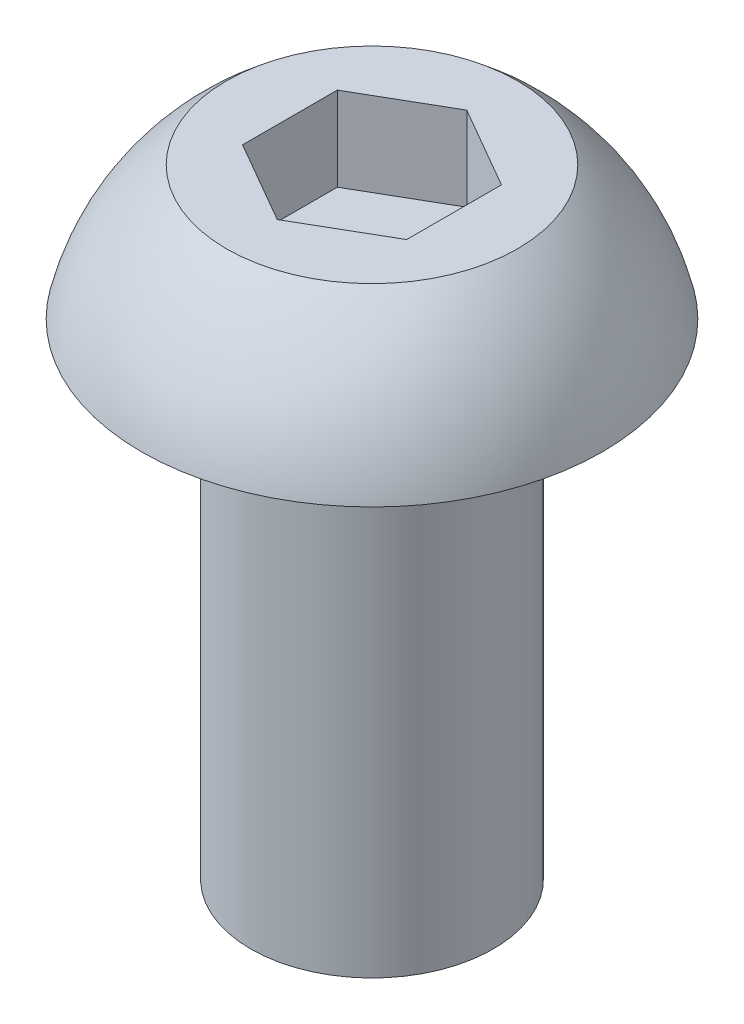
SolidWorks part; units mm, degrees
material "普通碳钢"
ref_plane "前视基准面" through (0, 0, 0) normal (0, 0, 1) x (1, 0, 0)
ref_plane "上视基准面" through (0, 0, 0) normal (0, 1, 0) x (1, 0, 0)
ref_plane "右视基准面" through (0, 0, 0) normal (1, 0, 0) x (0, 0, -1)
sketch "草图1" plane through (0, 0, 0) normal (0, 0, 1) x (1, 0, 0)
  line L0 (0, 2.3045) -> (-1.8, 2.3045)
  line L1 (0, 2.3045) -> (0, -5.3455)
  line L2 (-2.85, 0.6545) -> (-1.5, 0.6545)
  line L3 (0, -5.3455) -> (-1.5, -5.3455)
  line L4 (-1.5, -5.3455) -> (-1.5, 0.6545)
  line L5 (0, 0) -> (0, 50000) construction
  arc A0 (-1.8, 2.3045) -> (-2.85, 0.6545) centre (0, 0) ccw
  dimension "da" = 3.6
  dimension "dk" = 5.7
  dimension "d" = 3
  dimension "k" = 1.65
  dimension "L" = 6
revolve "旋转1" add sketch "草图1" angle 360 about L5
sketch "草图2" plane through (0, 2.3045, 0) normal (0, 1, 0) x (1, 0, 0)
  line L1 (0, -1.172) -> (1.015, -0.586)
  line L2 (1.015, -0.586) -> (1.015, 0.586)
  line L3 (1.015, 0.586) -> (0, 1.172)
  line L4 (0, 1.172) -> (-1.015, 0.586)
  line L5 (-1.015, 0.586) -> (-1.015, -0.586)
  line L6 (-1.015, -0.586) -> (0, -1.172)
  circle A0 centre (0, 0) radius 1.015 construction
  dimension "S" = 2.03
extrude "切除-拉伸1" cut sketch "草图2" against normal blind 1.04
fillet "圆角1" radius 0.1 1 edges at (0, 0.6545, -1.5)
